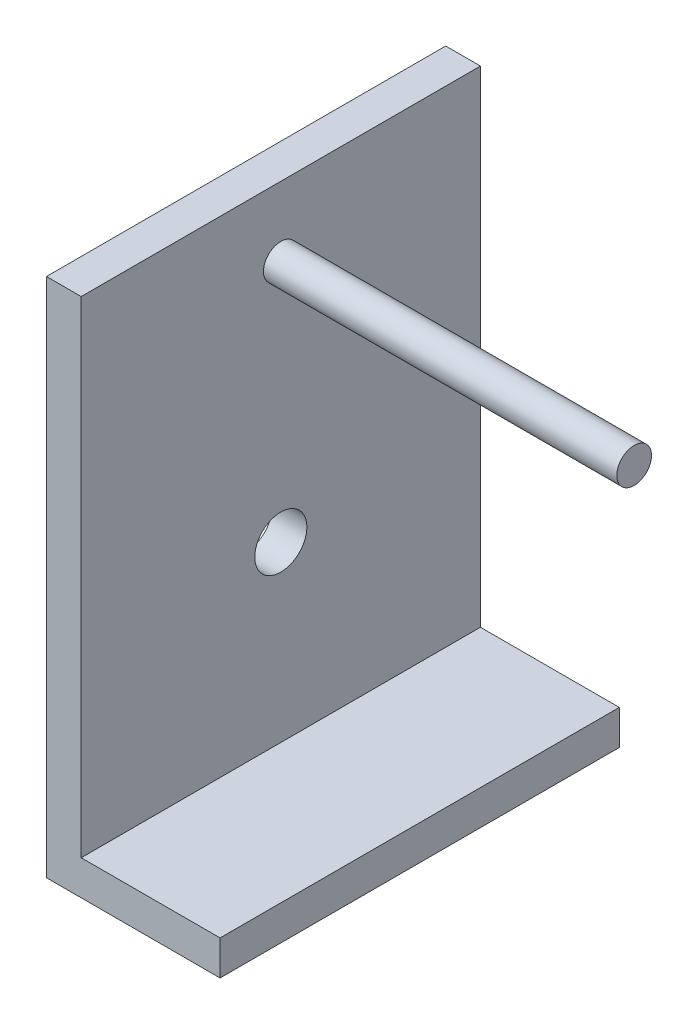
SolidWorks part; units mm, degrees
ref_plane "Front Plane" through (0, 0, 0) normal (0, 0, 1) x (1, 0, 0)
ref_plane "Top Plane" through (0, 0, 0) normal (0, 1, 0) x (1, 0, 0)
ref_plane "Right Plane" through (0, 0, 0) normal (1, 0, 0) x (0, 0, -1)
sketch "Sketch1" plane through (0, 0, 0) normal (0, 0, 1) x (1, 0, 0)
  line L0 (0, 150) -> (0, 0)
  line L1 (0, 0) -> (50, 0)
  line L2 (50, 0) -> (50, 10)
  line L3 (50, 10) -> (10, 10)
  line L4 (10, 10) -> (10, 150)
  line L5 (10, 150) -> (0, 150)
  line L6 (55, 0) -> (-55, 0) construction
  line L7 (0, -55) -> (0, 55) construction
  dimension "D1" = 10
  dimension "D2" = 10
  dimension "D3" = 150
  dimension "D4" = 50
extrude "Boss-Extrude1" add sketch "Sketch1" along normal mid plane 115
sketch "Sketch2" plane through (0, 0, 0) normal (-1, 0, 0) x (0, 0, 1)
  circle A0 centre (0, 60) radius 7.5
extrude "Cut-Extrude1" cut sketch "Sketch2" against normal through all
sketch "Sketch3" plane through (10, 0, 0) normal (1, 0, 0) x (0, 0, -1)
  line L0 (-57.5, 150) -> (57.5, 150) construction
  circle A0 centre (0, 130) radius 5
  dimension "D1" = 10
  dimension "D2" = 20
extrude "Boss-Extrude2" add sketch "Sketch3" along normal blind 101.7807
